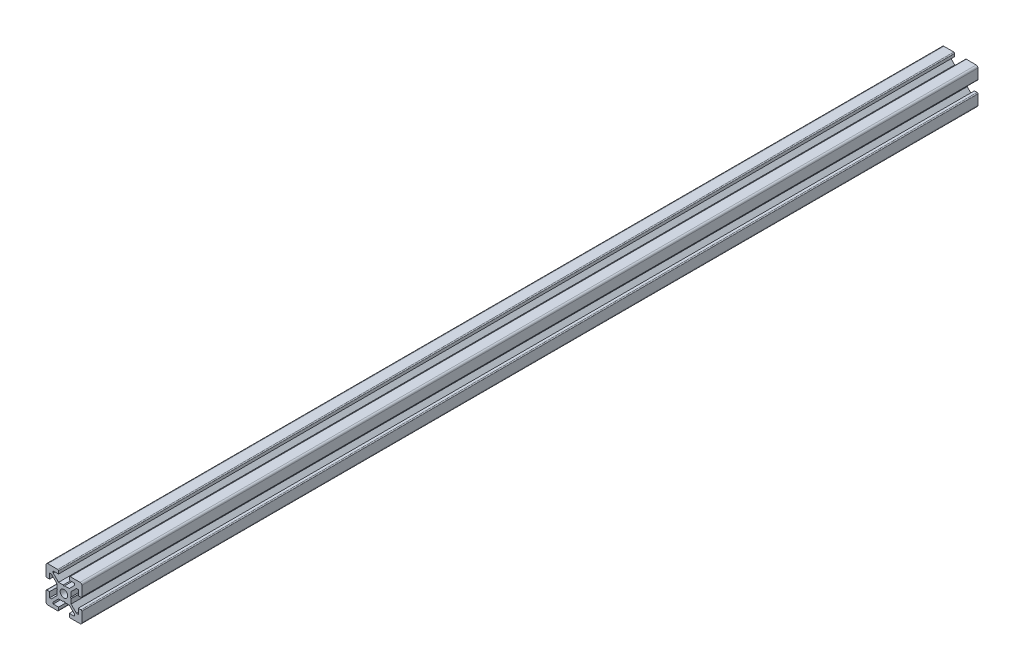
SolidWorks part; units mm, degrees
material "Lega 6061"
ref_plane "Piano frontale" through (0, 0, 0) normal (0, 0, 1) x (1, 0, 0)
ref_plane "Piano superiore" through (0, 0, 0) normal (0, 1, 0) x (1, 0, 0)
ref_plane "Piano destro" through (0, 0, 0) normal (1, 0, 0) x (0, 0, -1)
sketch "Schizzo1" plane through (0, 0, 0) normal (0, 0, 1) x (1, 0, 0)
  line L0 (0, 0) -> (-10, 0) construction
  line L1 (0, 0) -> (0, 10) construction
  line L2 (-3.6, 0) -> (-4, 0.4)
  line L3 (-4, 0.4) -> (-4, 3)
  line L4 (-4, 3) -> (-7, 6)
  line L5 (-7, 6) -> (-8, 6)
  line L6 (-8, 6) -> (-8, 3)
  line L7 (-8, 3) -> (-9.5, 3)
  line L8 (-10, 3.5) -> (-10, 9)
  line L9 (0, 0) -> (-10, 10) construction
  line L10 (0, 3.6) -> (-0.4, 4)
  line L11 (-0.4, 4) -> (-3, 4)
  line L12 (-3, 4) -> (-6, 7)
  line L13 (-6, 7) -> (-6, 8)
  line L14 (-6, 8) -> (-3, 8)
  line L15 (-3, 8) -> (-3, 9.5)
  line L16 (-3.5, 10) -> (-9, 10)
  line L17 (0, 0) -> (-10, -10) construction
  line L18 (-3.5, -10) -> (-9, -10)
  line L19 (-3, -8) -> (-3, -9.5)
  line L20 (-6, -8) -> (-3, -8)
  line L21 (-6, -7) -> (-6, -8)
  line L22 (-3, -4) -> (-6, -7)
  line L23 (-0.4, -4) -> (-3, -4)
  line L24 (0, -3.6) -> (-0.4, -4)
  line L25 (-10, -3.5) -> (-10, -9)
  line L26 (-8, -3) -> (-9.5, -3)
  line L27 (-8, -6) -> (-8, -3)
  line L28 (-7, -6) -> (-8, -6)
  line L29 (-4, -3) -> (-7, -6)
  line L30 (-4, -0.4) -> (-4, -3)
  line L31 (-3.6, 0) -> (-4, -0.4)
  line L32 (0, 0) -> (10, -10) construction
  line L33 (0, 0) -> (10, 10) construction
  line L34 (3.6, 0) -> (4, -0.4)
  line L35 (4, -0.4) -> (4, -3)
  line L36 (4, -3) -> (7, -6)
  line L37 (7, -6) -> (8, -6)
  line L38 (8, -6) -> (8, -3)
  line L39 (8, -3) -> (9.5, -3)
  line L40 (10, -3.5) -> (10, -9)
  line L41 (0, -3.6) -> (0.4, -4)
  line L42 (0.4, -4) -> (3, -4)
  line L43 (3, -4) -> (6, -7)
  line L44 (6, -7) -> (6, -8)
  line L45 (6, -8) -> (3, -8)
  line L46 (3, -8) -> (3, -9.5)
  line L47 (3.5, -10) -> (9, -10)
  line L48 (3.5, 10) -> (9, 10)
  line L49 (3, 8) -> (3, 9.5)
  line L50 (6, 8) -> (3, 8)
  line L51 (6, 7) -> (6, 8)
  line L52 (3, 4) -> (6, 7)
  line L53 (0.4, 4) -> (3, 4)
  line L54 (0, 3.6) -> (0.4, 4)
  line L55 (10, 3.5) -> (10, 9)
  line L56 (8, 3) -> (9.5, 3)
  line L57 (8, 6) -> (8, 3)
  line L58 (7, 6) -> (8, 6)
  line L59 (4, 3) -> (7, 6)
  line L60 (4, 0.4) -> (4, 3)
  line L61 (3.6, 0) -> (4, 0.4)
  arc A0 (-10, 9) -> (-9, 10) centre (-9, 9) cw
  arc A1 (-3, 9.5) -> (-3.5, 10) centre (-3.5, 9.5) ccw
  arc A2 (-9.5, 3) -> (-10, 3.5) centre (-9.5, 3.5) cw
  arc A3 (-9.5, -3) -> (-10, -3.5) centre (-9.5, -3.5) ccw
  arc A4 (-3, -9.5) -> (-3.5, -10) centre (-3.5, -9.5) cw
  arc A5 (-10, -9) -> (-9, -10) centre (-9, -9) ccw
  arc A6 (10, -9) -> (9, -10) centre (9, -9) cw
  arc A7 (3, -9.5) -> (3.5, -10) centre (3.5, -9.5) ccw
  arc A8 (9.5, -3) -> (10, -3.5) centre (9.5, -3.5) cw
  arc A9 (9.5, 3) -> (10, 3.5) centre (9.5, 3.5) ccw
  arc A10 (3, 9.5) -> (3.5, 10) centre (3.5, 9.5) cw
  arc A11 (10, 9) -> (9, 10) centre (9, 9) ccw
  circle A12 centre (0, 0) radius 2.1
  point P24 (-3, 10)
  point P27 (-10, 3)
  point P49 (-10, -3)
  point P50 (-3, -10)
  point P92 (3, -10)
  point P93 (10, -3)
  point P94 (10, 3)
  point P95 (3, 10)
  dimension "D2" = 1
  dimension "D12" = 0.5
  dimension "D13" = 4.2
  dimension "D3" = 8
  dimension "D4" = 0.4
  dimension "D5" = 45
  dimension "D6" = 6
  dimension "D7" = 12
  dimension "D8" = 20
  dimension "D9" = 2
  dimension "D10" = 4
  dimension "D11" = 45
extrude "Estrusione-Estrusione1" add sketch "Schizzo1" along normal blind 500
